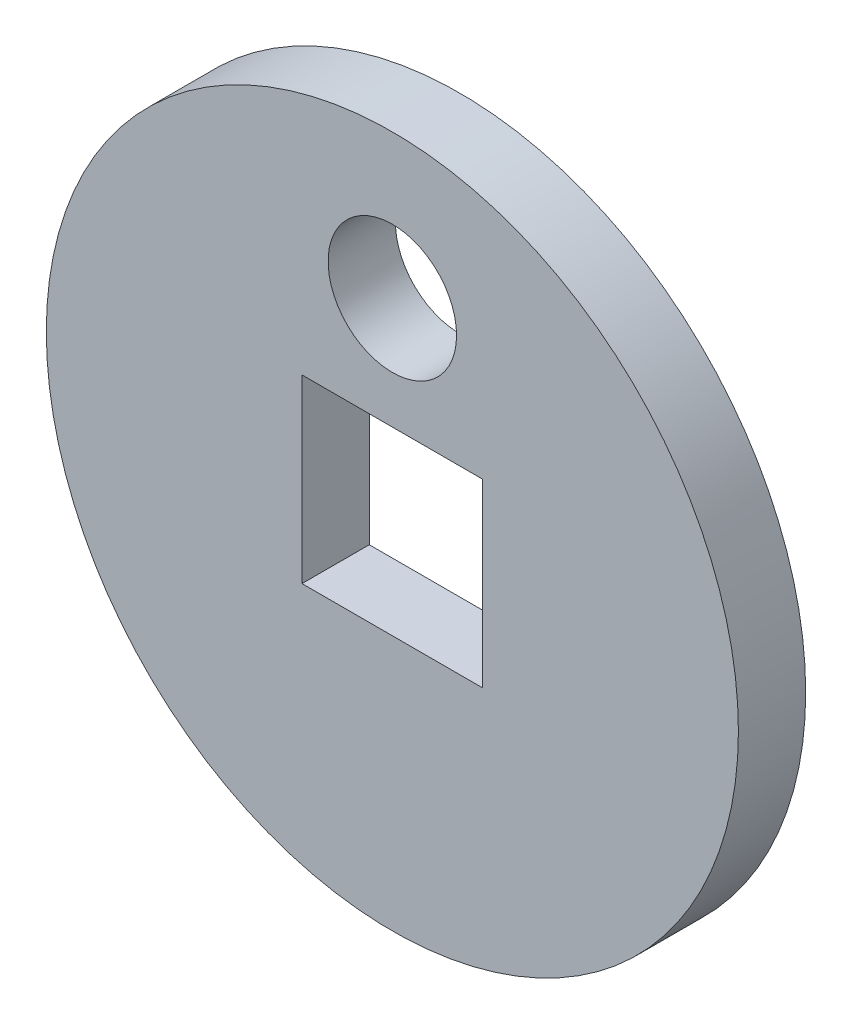
SolidWorks part; units mm, degrees
ref_plane "Front Plane" through (0, 0, 0) normal (0, 0, 1) x (1, 0, 0)
ref_plane "Top Plane" through (0, 0, 0) normal (0, 1, 0) x (1, 0, 0)
ref_plane "Right Plane" through (0, 0, 0) normal (1, 0, 0) x (0, 0, -1)
sketch "Sketch1" plane through (0, 0, 0) normal (0, 0, 1) x (1, 0, 0)
  circle A0 centre (0, 0) radius 9
extrude "Boss-Extrude1" add sketch "Sketch1" along normal blind 1.75
sketch "Sketch2" plane through (0, 0, 1.75) normal (0, 0, 1) x (1, 0, 0)
  line L1 (-2.35, -2.35) -> (2.35, -2.35)
  line L2 (-2.35, -2.35) -> (-2.35, 2.35)
  line L3 (-2.35, 2.35) -> (2.35, 2.35)
  line L4 (2.35, -2.35) -> (2.35, 2.35)
  line L5 (-2.35, -2.35) -> (2.35, 2.35) construction
  line L6 (-2.35, 2.35) -> (2.35, -2.35) construction
  circle A0 centre (0, 5.25) radius 1.67
  point P0 (0, 0)
  dimension "D1" = 4.7
  dimension "D2" = 4.7
extrude "Cut-Extrude1" cut sketch "Sketch2" against normal through all
